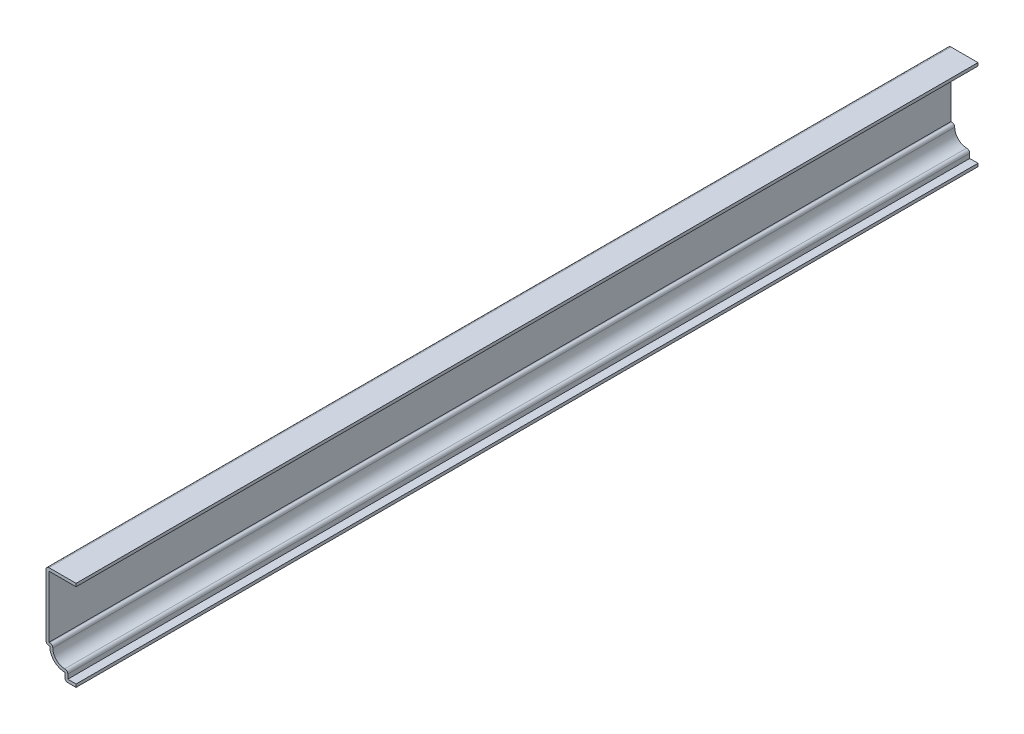
SolidWorks part; units mm, degrees
ref_plane "Front Plane" through (0, 0, 0) normal (0, 0, 1) x (1, 0, 0)
ref_plane "Top Plane" through (0, 0, 0) normal (0, 1, 0) x (1, 0, 0)
ref_plane "Right Plane" through (0, 0, 0) normal (1, 0, 0) x (0, 0, -1)
sketch "Sketch1" plane through (0, 0, 0) normal (0, 0, 1) x (1, 0, 0)
  line L0 (0, 0) -> (-4.7625, 0)
  line L1 (-4.7625, 0) -> (-4.7625, 3.175)
  line L2 (-11.1125, 9.525) -> (-12.7, 9.525)
  line L3 (-12.7, 9.525) -> (-12.7, 38.1)
  line L4 (-12.7, 38.1) -> (0, 38.1)
  arc A0 (-4.7625, 3.175) -> (-11.1125, 9.525) centre (-4.7625, 9.525) cw
  dimension "D1" = 12.7
  dimension "D2" = 4.7625
  dimension "D3" = 3.175
  dimension "D4" = 6.35
  dimension "D5" = 1.5875
  dimension "D6" = 28.575
extrude "Extrude-Thin1" add sketch "Sketch1" against normal blind 381 thin
fillet "Fillet1" radius 1.27 5 edges at (-12.7, 38.1, -190.5) (-4.7625, 0, -190.5) (-12.7, 9.525, -190.5) (-9.6812, 10.795, -190.5) (-3.4925, 4.6063, -190.5)
